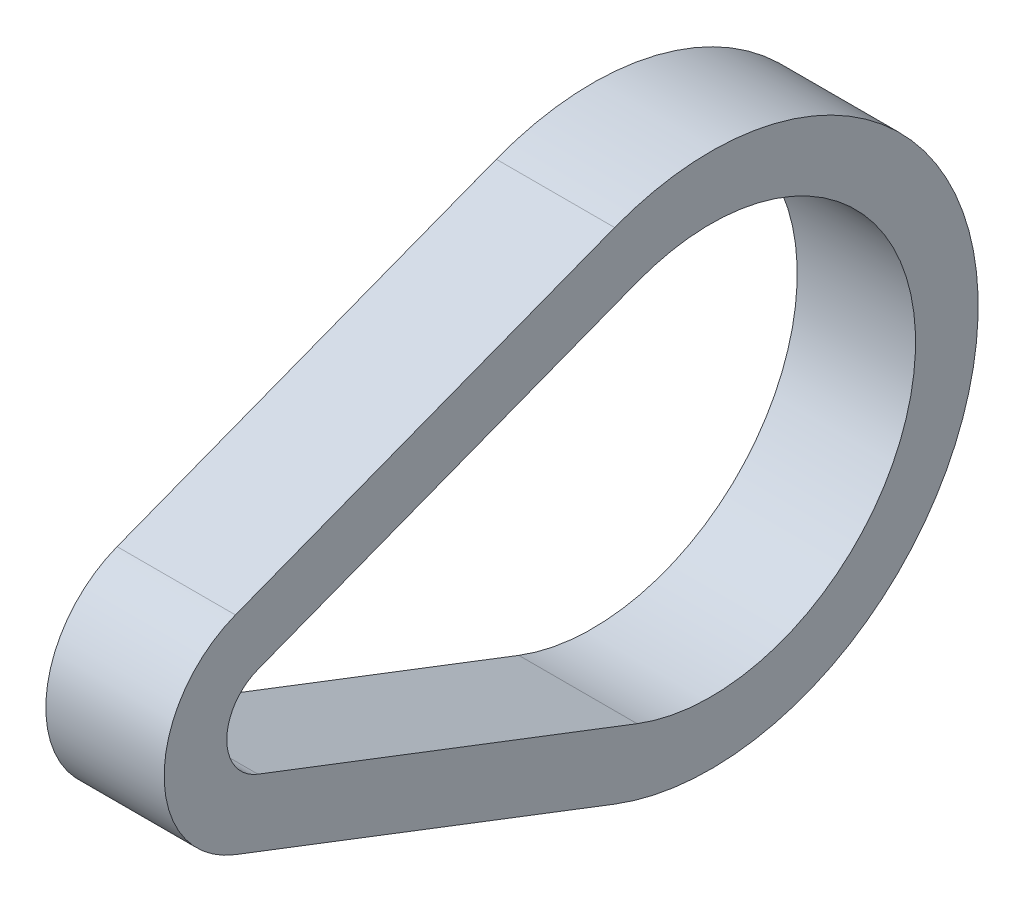
SolidWorks part; units mm, degrees
ref_plane "Front Plane" through (0, 0, 0) normal (0, 0, 1) x (1, 0, 0)
ref_plane "Top Plane" through (0, 0, 0) normal (0, 1, 0) x (1, 0, 0)
ref_plane "Right Plane" through (0, 0, 0) normal (1, 0, 0) x (0, 0, -1)
other "Bounding Box"
ref_plane "Default Plane" through (-8.9266, -12.7485, 0) normal (-0.1736, 0.9848, 0) x (0.9848, 0.1736, 0)
sketch "Sketch1" plane through (0, 0, 0) normal (1, 0, 0) x (0, 0, -1)
  line L0 (0, 0) -> (22.0726, 0) construction
  line L1 (-0.8846, 2.2995) -> (18.3427, 9.6959)
  line L2 (-0.8846, -2.2995) -> (18.3427, -9.6959)
  line L3 (-2.0245, 5.2628) -> (17.2028, 12.6592)
  line L4 (-2.0245, -5.2628) -> (17.2028, -12.6592)
  arc A0 (-0.8846, 2.2995) -> (-0.8846, -2.2995) centre (0, 0) ccw
  arc A1 (18.3427, -9.6959) -> (18.3427, 9.6959) centre (22.0726, 0) ccw
  arc A2 (-2.0245, 5.2628) -> (-2.0245, -5.2628) centre (0, 0) ccw
  arc A3 (17.2028, -12.6592) -> (17.2028, 12.6592) centre (22.0726, 0) ccw
  dimension "D2" = 3.175
  dimension "D3" = 3.175
  dimension "D4" = 4.9276
  dimension "D5" = 20.7772
  dimension "D1" = 22.0726
extrude "Boss-Extrude1" add sketch "Sketch1" along normal mid plane 6
